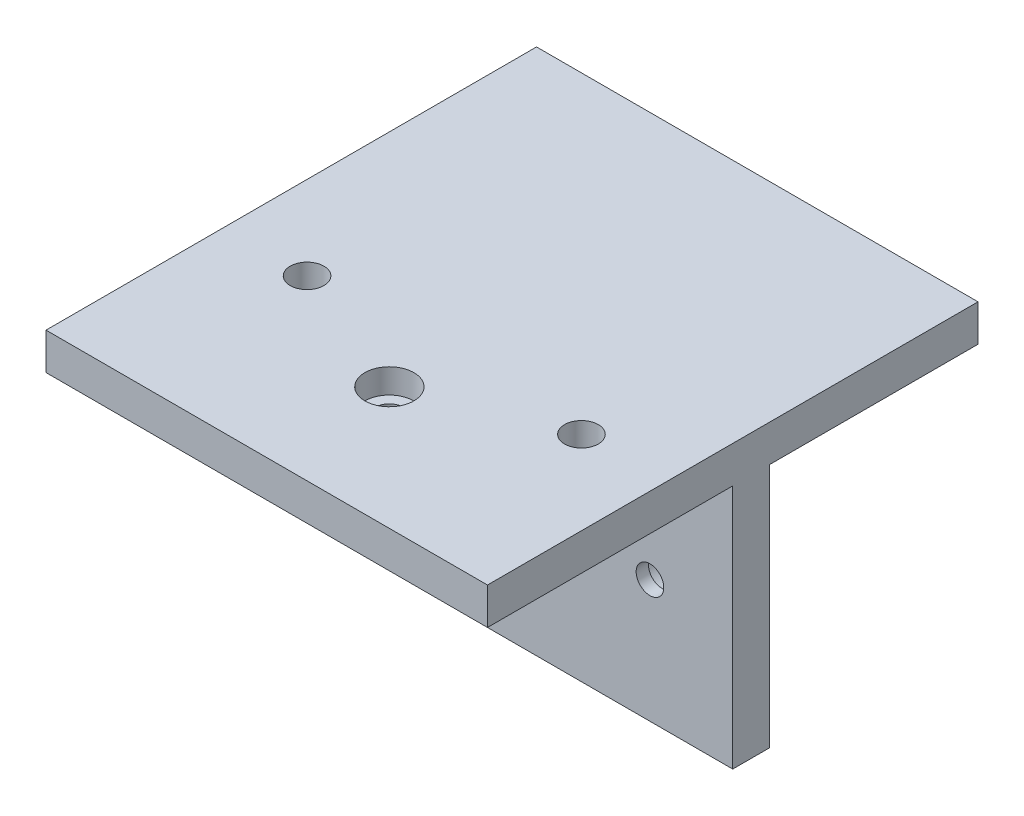
SolidWorks part; units mm, degrees
ref_plane "Front Plane" through (0, 0, 0) normal (0, 0, 1) x (1, 0, 0)
ref_plane "Top Plane" through (0, 0, 0) normal (0, 1, 0) x (1, 0, 0)
ref_plane "Right Plane" through (0, 0, 0) normal (1, 0, 0) x (0, 0, -1)
sketch "Sketch1" plane through (0, 0, 0) normal (1, 0, 0) x (0, 0, -1)
  line L0 (-20, 20) -> (20, 20)
  line L1 (-20, 20) -> (20, 20) construction
  line L2 (-20, 20) -> (-20, -20) construction
  line L3 (-20, -20) -> (20, -20) construction
  line L4 (20, 20) -> (20, -20) construction
  line L5 (-20, 20) -> (20, -20) construction
  line L6 (-20, -20) -> (20, 20) construction
  line L7 (20, 20) -> (20, -20)
  line L8 (26, 20) -> (60, 20)
  line L10 (-20, 20) -> (-20, 26)
  line L11 (-20, 26) -> (60, 26)
  line L12 (60, 26) -> (60, 20)
  line L13 (20, -20) -> (26, -20)
  line L14 (26, -20) -> (26, 20)
  point P0 (0, 0)
  dimension "D1" = 40
  dimension "D2" = 40
  dimension "D3" = 6
  dimension "D4" = 6
extrude "Boss-Extrude1" add sketch "Sketch1" along normal mid plane 72 contours L12 L11 L10 L0 L8
sketch "Sketch2" plane through (0, 0, -26) normal (0, 0, -1) x (-1, 0, 0)
  line L0 (-22.5, 20) -> (-22.5, -20) construction
  line L1 (-36, 20) -> (36, 20) construction
  line L2 (-36, -20) -> (36, -20) construction
  line L3 (22.5, 20) -> (22.5, -20) construction
  line L4 (-36, 20) -> (36, 20) construction
  line L6 (22.5, -20) -> (-22.5, -20) construction
  circle A0 centre (-22.5, 0) radius 2.25
  circle A1 centre (22.5, 0) radius 2.25
  point P10 (0, -20)
  dimension "D2" = 4.5
  dimension "D1" = 45
extrude "Cut-Extrude1" cut sketch "Sketch2" against normal up to next
sketch "Sketch3" plane through (0, 20, 0) normal (0, -1, 0) x (1, 0, 0)
  circle A0 centre (0, 0) radius 2.25
  dimension "D2" = 4.5
extrude "Cut-Extrude2" cut sketch "Sketch3" against normal up to next
sketch "Sketch4" plane through (0, 0, -26) normal (0, 0, -1) x (-1, 0, 0)
  circle A0 centre (-22.5, 0) radius 4
  circle A1 centre (22.5, 0) radius 4
  dimension "D1" = 8
extrude "Cut-Extrude3" cut sketch "Sketch4" against normal blind 4
sketch "Sketch5" plane through (0, 26, 0) normal (0, 1, 0) x (1, 0, 0)
  circle A1 centre (0, 0) radius 4
  dimension "D1" = 8
extrude "Cut-Extrude4" cut sketch "Sketch5" against normal blind 4
sketch "Sketch7" plane through (0, 26, 0) normal (0, 1, 0) x (1, 0, 0)
  line L0 (-22.375, 8.95) -> (22.375, 8.95) construction
  circle A0 centre (-22.375, 8.95) radius 2.25
  circle A1 centre (22.375, 8.95) radius 2.25
  point P2 (0, 8.95)
  dimension "D3" = 4.5
  dimension "D1" = 44.75
  dimension "D2" = 8.95
extrude "Cut-Extrude5" cut sketch "Sketch7" against normal up to next
sketch "Sketch8" plane through (0, 26, 0) normal (0, 1, 0) x (1, 0, 0)
  circle A0 centre (-22.375, 8.95) radius 2.75
  circle A1 centre (22.375, 8.95) radius 2.75
  dimension "D1" = 5.5
extrude "Cut-Extrude6" cut sketch "Sketch8" against normal blind 4
sketch "Sketch9" plane through (0, 0, 0) normal (1, 0, 0) x (0, 0, -1)
  line L0 (26, -20) -> (60, 20)
  line L1 (26, -20) -> (26, 20)
  line L2 (26, 20) -> (60, 20)
extrude "Boss-Extrude2" add sketch "Sketch9" along normal mid plane 6
equation "\"ClearHole\"=4.5"
equation "\"D2@Sketch2\"=\"ClearHole\""
equation "\"D2@Sketch3\"=\"ClearHole\""
equation "\"SocketClear\"=8"
equation "\"D1@Sketch4\"=\"SocketClear\""
equation "\"SocketDepth\"=4"
equation "\"D1@Cut-Extrude3\"=\"SocketDepth\""
equation "\"D4@Sketch1\"=\"D3@Sketch1\""
equation "\"Thicknes\"=6"
equation "\"D3@Sketch1\"=\"Thicknes\""
equation "\"D1@Sketch5\"=\"SocketClear\""
equation "\"D3@Sketch7\"=\"ClearHole\""
equation "\"MFourInsert\"=5.5"
equation "\"D1@Sketch8\"=\"MFourInsert\""
